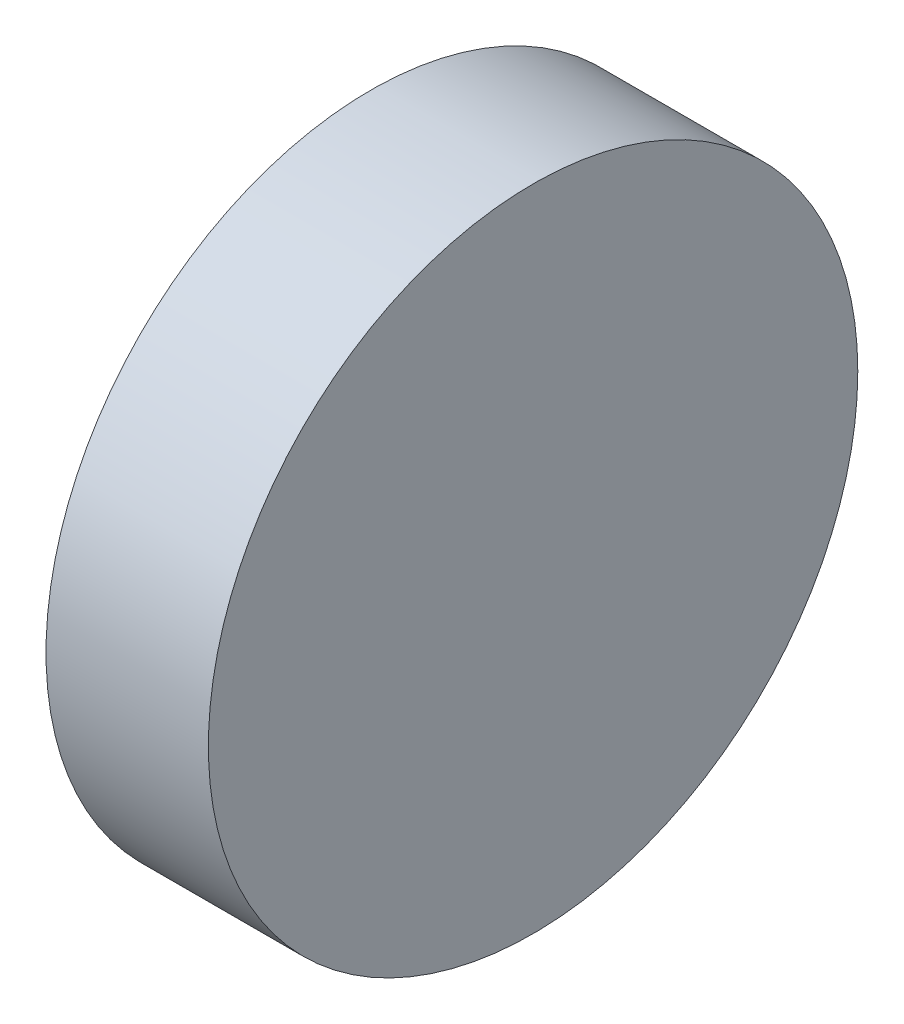
SolidWorks part; units mm, degrees
ref_plane "Front Plane" through (0, 0, 0) normal (0, 0, 1) x (1, 0, 0)
ref_plane "Top Plane" through (0, 0, 0) normal (0, 1, 0) x (1, 0, 0)
ref_plane "Right Plane" through (0, 0, 0) normal (1, 0, 0) x (0, 0, -1)
sketch "Sketch2" plane through (3109.4197, 0, 0) normal (1, 0, 0) x (0, 0, -1)
  circle A0 centre (50.3393, -50.5544) radius 600
  dimension "D1" = 1200
extrude "Extrude1" add sketch "Sketch2" along normal blind 300
